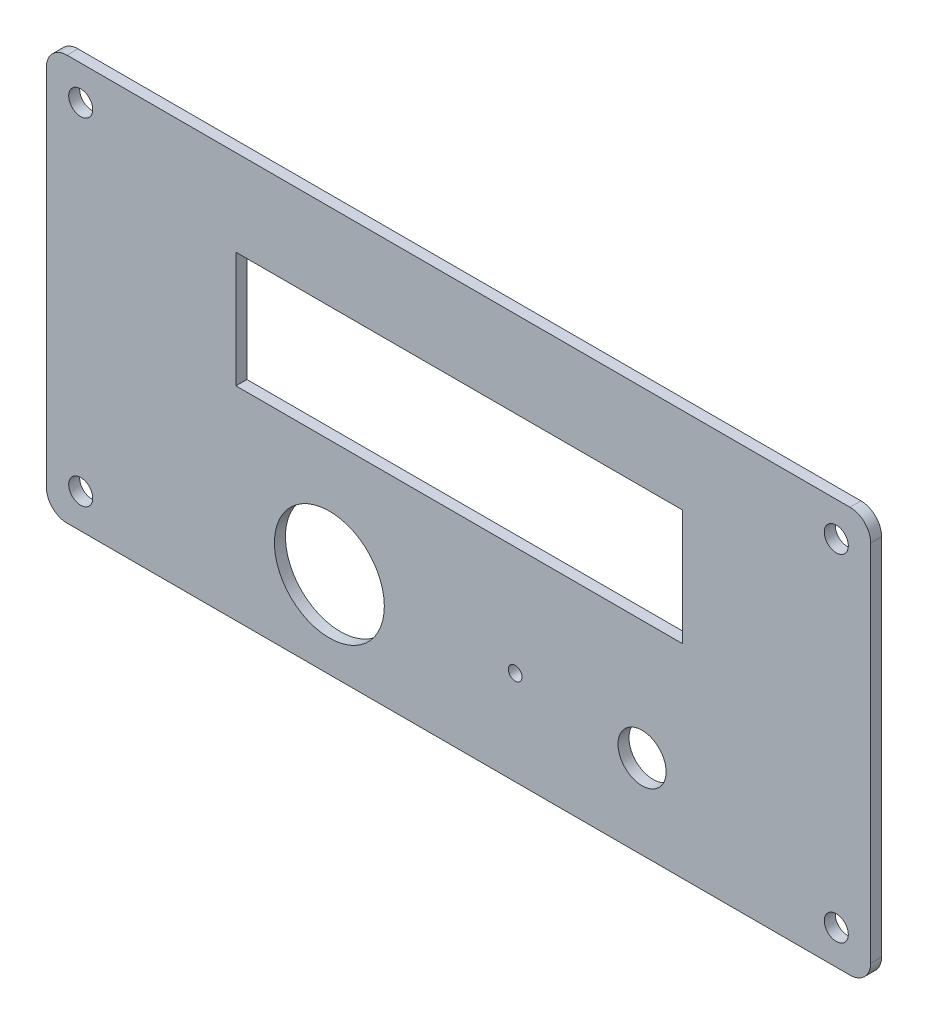
SolidWorks part; units mm, degrees
material "氧化铝"
ref_plane "前视基准面" through (0, 0, 0) normal (0, 0, 1) x (1, 0, 0)
ref_plane "上视基准面" through (0, 0, 0) normal (0, 1, 0) x (1, 0, 0)
ref_plane "右视基准面" through (0, 0, 0) normal (1, 0, 0) x (0, 0, -1)
sketch "草图1" plane through (0, 0, 0) normal (0, 0, 1) x (1, 0, 0)
  line L0 (-60, 3.5732) -> (43.9654, 3.5732) construction
  line L1 (-57, 33.0732) -> (57, 33.0732)
  line L2 (-60, 30.0732) -> (-60, -22.9268)
  line L3 (-57, -25.9268) -> (57, -25.9268)
  line L4 (60, 30.0732) -> (60, -22.9268)
  line L5 (14.3783, 3.8236) -> (14.3783, 20.6736)
  line L6 (0, 33.0732) -> (0, -33.0732) construction
  line L7 (-32.4026, 20.5275) -> (32.5974, 20.5275)
  line L8 (-32.4026, 20.5275) -> (-32.4026, 3.6775)
  line L9 (-32.4026, 3.6775) -> (32.5974, 3.6775)
  line L10 (32.5974, 20.5275) -> (32.5974, 3.6775)
  line L11 (-32.4026, 20.5275) -> (32.5974, 3.6775) construction
  line L12 (-32.4026, 3.6775) -> (32.5974, 20.5275) construction
  circle A0 centre (-55, -20.9268) radius 1.75
  arc A1 (-60, -22.9268) -> (-57, -25.9268) centre (-57, -22.9268) ccw
  arc A2 (57, -25.9268) -> (60, -22.9268) centre (57, -22.9268) ccw
  arc A3 (57, 33.0732) -> (60, 30.0732) centre (57, 30.0732) cw
  arc A4 (-57, 33.0732) -> (-60, 30.0732) centre (-57, 30.0732) ccw
  circle A5 centre (55, -20.9268) radius 1.75
  circle A6 centre (55, 28.0732) radius 1.75
  circle A7 centre (-55, 28.0732) radius 1.75
  circle A8 centre (26.7211, -13.6825) radius 3.5
  circle A9 centre (-18.7989, -13.3125) radius 8
  circle A10 centre (8.2511, -12.2225) radius 1
  point P20 (0.0974, 12.1025)
  dimension "D1" = 3.5
  dimension "D2" = 3
  dimension "D8" = 16
  dimension "D10" = 2
  dimension "D12" = 7
  dimension "D3" = 5
  dimension "D4" = 5
  dimension "D5" = 16.85
  dimension "D6" = 65
  dimension "D7" = 16.99
  dimension "D9" = 15.9
  dimension "D11" = 17.36
  dimension "D13" = 13.6037
  dimension "D14" = 40.6537
  dimension "D15" = 5.8763
extrude "凸台-拉伸1" add sketch "草图1" along normal blind 1.6
